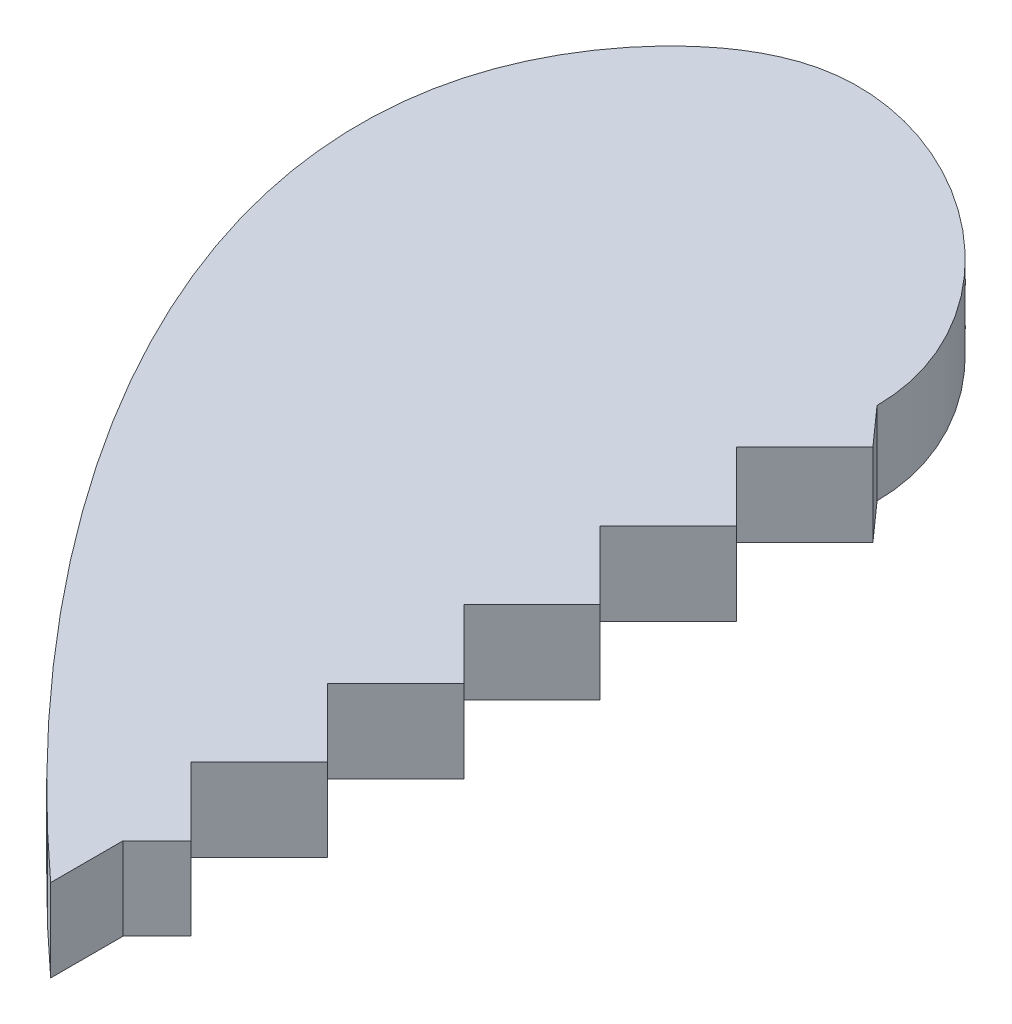
SolidWorks part; units mm, degrees
ref_plane "Front Plane" through (0, 0, 0) normal (0, 0, 1) x (1, 0, 0)
ref_plane "Top Plane" through (0, 0, 0) normal (0, 1, 0) x (1, 0, 0)
ref_plane "Right Plane" through (0, 0, 0) normal (1, 0, 0) x (0, 0, -1)
sketch "Sketch1" plane through (0, 0, 0) normal (0, 1, 0) x (1, 0, 0)
  line L0 (0, 14.0721) -> (0, -15.9279) construction
  line L1 (0, 10.7544) -> (0, 1.5585) construction
  line L2 (0, -55) -> (0, 55) construction
  spline S0 degree 3 poles (0, 14.0721) (0, 19.2449) (9.4205, 26.7564) (24.9138, 13.2722) (11.533, -5.4546) (0, -15.9279) knots 0 0 0 0 0.261667 0.361667 1 1 1 1
  spline S1 degree 3 poles (0, 14.0721) (0, 19.2449) (-9.4205, 26.7564) (-24.9138, 13.2722) (-11.533, -5.4546) (0, -15.9279) knots 0 0 0 0 0.261667 0.361667 1 1 1 1
  point P6 (0, 0)
  point P7 (0, 0)
  point P8 (0, 0)
  dimension "D1" = 30
extrude "Boss-Extrude1" add sketch "Sketch1" along normal blind 3
sketch "Sketch2" plane through (0, 3, 0) normal (0, 1, 0) x (1, 0, 0)
  line L0 (0, 14.0721) -> (1.2374, 12.684)
  line L1 (1.2374, -12.0648) -> (-1.2374, -14.5397)
  line L2 (1.2374, 12.684) -> (-1.2374, 10.2091)
  line L3 (-1.2374, 10.2091) -> (1.2374, 7.7342)
  line L4 (1.2374, 7.7342) -> (-1.2374, 5.2593)
  line L5 (-1.2374, 5.2593) -> (1.2374, 2.7845)
  line L6 (1.2374, 2.7845) -> (-1.2374, 0.3096)
  line L7 (-1.2374, 0.3096) -> (1.2374, -2.1653)
  line L8 (1.2374, -2.1653) -> (-1.2374, -4.6402)
  line L9 (-1.2374, -4.6402) -> (1.2374, -7.115)
  line L10 (1.2374, -7.115) -> (-1.2374, -9.5899)
  line L11 (-1.2374, -9.5899) -> (1.2374, -12.0648)
  line L12 (-1.2374, -14.5397) -> (0, -15.9279)
  line L13 (0, 14.0721) -> (0, -15.9279) construction
  spline S1 degree 3 poles (1514.8716, 1288.2661) (-463.8444, -281.802) (69.1877, -25.2608) (-11.6473, 45.0923) (-124.7996, -212.365) (1789.1499, 901.4783) knots -2.857633 -2.857633 -2.857633 -2.857633 0.638333 0.738333 2.359809 2.359809 2.359809 2.359809 only from (0, -15.9279) to (0, 14.0721) construction
  spline S2 degree 3 poles (0, -15.9279) (11.533, -5.4546) (24.9138, 13.2722) (9.4205, 26.7564) (0, 19.2449) (0, 14.0721) knots 0 0 0 0 0.638333 0.738333 1 1 1 1 construction
  spline S3 degree 3 poles (-1789.1544, 901.4809) (124.7997, -212.3654) (11.6473, 45.0924) (-69.1878, -25.2608) (463.845, -281.8022) (-1514.8746, 1288.2685) knots -1.35981 -1.35981 -1.35981 -1.35981 0.261667 0.361667 3.857635 3.857635 3.857635 3.857635 only from (0, 14.0721) to (0, -15.9279) construction
  spline S4 degree 3 poles (0, 14.0721) (0, 14.0723) (0, 14.0724) (0, 14.0725) knots 0 0 0 0 0.000006 0.000006 0.000006 0.000006
  spline S7 degree 3 poles (-2648.8668, 1411.9302) (154.0023, -280.0848) (14.9342, 47.953) (-75.4194, -30.6844) (590.452, -341.7944) (-2301.6412, 1905.5069) knots -1.57196 -1.57196 -1.57196 -1.57196 0.261667 0.361667 4.259851 4.259851 4.259851 4.259851 only from (0, 14.0721) to (0, -15.9279)
  spline S8 degree 3 poles (2301.6005, 1905.4753) (-590.4459, -341.7915) (75.4191, -30.6841) (-14.9346, 47.9534) (-154.0061, -280.0936) (2648.9864, 1412.0024) knots -3.259833 -3.259833 -3.259833 -3.259833 0.638333 0.738333 2.571986 2.571986 2.571986 2.571986 only from (0, -15.9279) to (0, 14.0721)
  spline S9 degree 3 poles (0, 14.0721) (0, 14.0723) (0, 14.0724) (0, 14.0725) knots 0 0 0 0 0.000006 0.000006 0.000006 0.000006
  spline S10 degree 3 poles (0, -15.9279) (11.533, -5.4546) (24.9138, 13.2722) (9.4205, 26.7564) (0, 19.2449) (0, 14.0721) knots 0 0 0 0 0.638333 0.738333 1 1 1 1
  point P17 (0, 11.4465)
  point P18 (0, -10.8274)
  dimension "D1" = 3.5
  dimension "D2" = 0
sketch "Sketch3" plane through (0, 3, 0) normal (0, 1, 0) x (1, 0, 0)
  line L1 (0, 14.0721) -> (1.2374, 12.684)
  line L2 (1.2374, 12.684) -> (-1.2374, 10.2091)
  line L3 (-1.2374, 10.2091) -> (1.2374, 7.7342)
  line L4 (1.2374, 7.7342) -> (-1.2374, 5.2593)
  line L5 (-1.2374, 5.2593) -> (1.2374, 2.7845)
  line L6 (1.2374, 2.7845) -> (-1.2374, 0.3096)
  line L7 (-1.2374, 0.3096) -> (1.2374, -2.1653)
  line L8 (1.2374, -2.1653) -> (-1.2374, -4.6402)
  line L9 (-1.2374, -4.6402) -> (1.2374, -7.115)
  line L10 (1.2374, -7.115) -> (-1.2374, -9.5899)
  line L11 (-1.2374, -9.5899) -> (1.2374, -12.0648)
  line L12 (1.2374, -12.0648) -> (0, -13.3022)
  line L13 (1.2374, -12.0648) -> (-1.2374, -14.5397) construction
  line L14 (0, -13.3022) -> (0, -15.9279)
  spline S0 degree 3 poles (2301.6005, 1905.4753) (-590.4459, -341.7915) (75.4191, -30.6841) (-14.9346, 47.9534) (-154.0061, -280.0936) (2648.9864, 1412.0024) knots -3.259833 -3.259833 -3.259833 -3.259833 0.638333 0.738333 2.571986 2.571986 2.571986 2.571986 only from (0, -15.9279) to (0, 14.0721) construction
  spline S1 degree 3 poles (0, -15.9279) (11.533, -5.4546) (24.9138, 13.2722) (9.4205, 26.7564) (0, 19.2449) (0, 14.0721) knots 0 0 0 0 0.638333 0.738333 1 1 1 1
extrude "Cut-Extrude1" cut sketch "Sketch3" against normal blind 3
